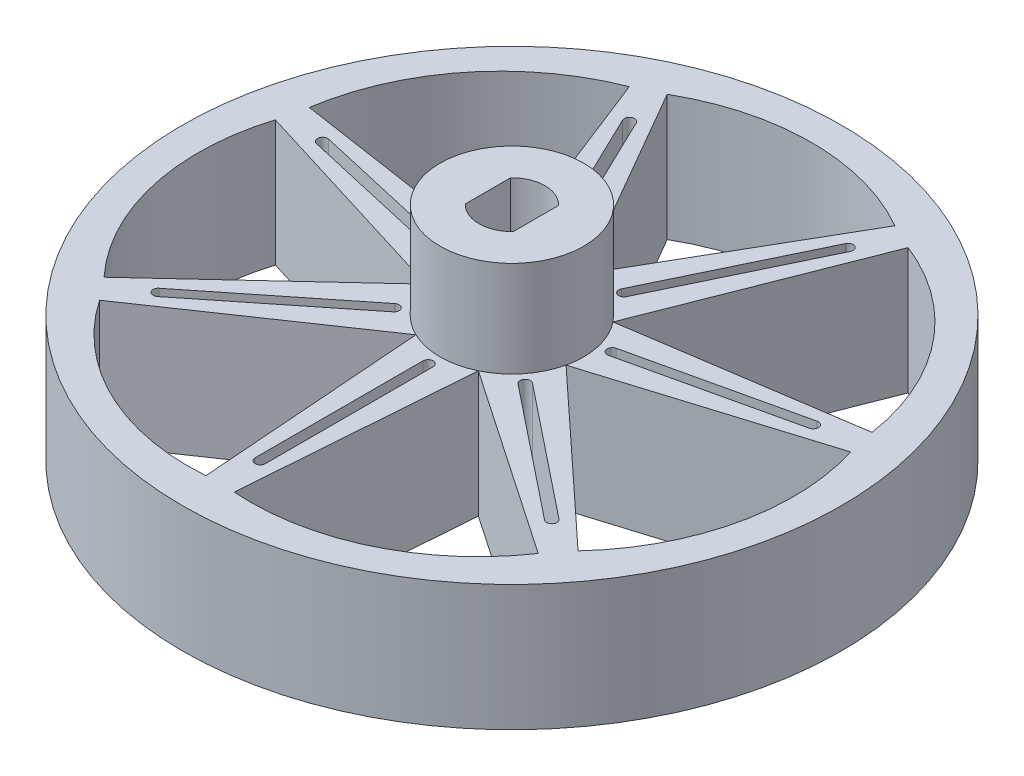
SolidWorks part; units mm, degrees
ref_plane "Front Plane" through (0, 0, 0) normal (0, 0, 1) x (1, 0, 0)
ref_plane "Top Plane" through (0, 0, 0) normal (0, 1, 0) x (1, 0, 0)
ref_plane "Right Plane" through (0, 0, 0) normal (1, 0, 0) x (0, 0, -1)
sketch "Sketch2" plane through (0, 0, 0) normal (0, 1, 0) x (1, 0, 0)
  line L0 (-2, -1.8875) -> (-2, 1.8875)
  line L2 (-1.75, -1.7854) -> (-1.75, 1.7854)
  line L4 (1.75, -1.7854) -> (1.75, 1.7854)
  line L5 (-1.75, -1.7854) -> (1.75, 1.7854) construction
  line L6 (-1.75, 1.7854) -> (1.75, -1.7854) construction
  line L7 (2, -1.8875) -> (2, 1.8875)
  arc A0 (1.75, 1.7854) -> (-1.75, 1.7854) centre (0, 0) ccw
  arc A1 (-1.75, -1.7854) -> (1.75, -1.7854) centre (0, 0) ccw
  circle A2 centre (0, 0) radius 6
  arc A3 (2, 1.8875) -> (-2, 1.8875) centre (0, 0) ccw
  arc A4 (-2, -1.8875) -> (2, -1.8875) centre (0, 0) ccw
  dimension "D1" = 5
  dimension "D3" = 12
  dimension "D2" = 3.5
  dimension "D4" = 0.25
extrude "Boss-Extrude1" add sketch "Sketch2" along normal blind 8 contours A2 A4 L0 A3 L7
sketch "Sketch3" plane through (0, 0, 0) normal (0, 1, 0) x (1, 0, 0)
  line L0 (0, 0) -> (0, 27.5) construction
  line L1 (0, 6) -> (9.5, 22.4545)
  line L2 (0, 6) -> (-9.5, 22.4545)
  line L3 (4.691, 3.7409) -> (11.6325, 21.4275)
  line L4 (4.691, 3.7409) -> (23.4788, 6.5727)
  line L5 (5.8496, -1.3351) -> (24.0055, 4.2652)
  line L6 (5.8496, -1.3351) -> (19.7776, -14.2584)
  line L7 (2.6033, -5.4058) -> (18.3018, -16.1089)
  line L8 (2.6033, -5.4058) -> (1.1834, -24.3527)
  line L9 (-2.6033, -5.4058) -> (-1.1834, -24.3527)
  line L10 (-2.6033, -5.4058) -> (-18.3018, -16.1089)
  line L11 (-5.8496, -1.3351) -> (-19.7776, -14.2584)
  line L12 (-5.8496, -1.3351) -> (-24.0055, 4.2652)
  line L13 (-4.691, 3.7409) -> (-23.4788, 6.5727)
  line L14 (-4.691, 3.7409) -> (-11.6325, 21.4275)
  circle A0 centre (0, 0) radius 1.375
  circle A1 centre (0, 0) radius 27.5
  circle A2 centre (0, 0) radius 6 construction
  arc A3 (9.5, 22.4545) -> (-9.5, 22.4545) centre (0, 6) ccw
  arc A4 (23.4788, 6.5727) -> (11.6325, 21.4275) centre (4.691, 3.7409) ccw
  arc A5 (19.7776, -14.2584) -> (24.0055, 4.2652) centre (5.8496, -1.3351) ccw
  arc A6 (1.1834, -24.3527) -> (18.3018, -16.1089) centre (2.6033, -5.4058) ccw
  arc A7 (-18.3018, -16.1089) -> (-1.1834, -24.3527) centre (-2.6033, -5.4058) ccw
  arc A8 (-24.0055, 4.2652) -> (-19.7776, -14.2584) centre (-5.8496, -1.3351) ccw
  arc A9 (-11.6325, 21.4275) -> (-23.4788, 6.5727) centre (-4.691, 3.7409) ccw
  point P37 (0, 0)
  dimension "D1" = 2.75
  dimension "D2" = 55
  dimension "D3" = 19
  dimension "D4" = 30
  dimension "D5" = 7
extrude "Boss-Extrude2" add sketch "Sketch3" against normal blind 10.5
sketch "Sketch4" plane through (0, -10.5, 0) normal (0, -1, 0) x (-1, 0, 0)
  circle A0 centre (0, 0) radius 3
  dimension "D1" = 6
extrude "Cut-Extrude1" cut sketch "Sketch4" against normal blind 9.5
sketch "Sketch5" plane through (0, 0, 0) normal (0, 1, 0) x (1, 0, 0)
  line L0 (0, -30.3767) -> (0, 0) construction
  line L1 (-5.7393, -4.0303) -> (-16.6849, -12.7592)
  line L2 (0.4274, -7) -> (-0.4274, -7)
  line L3 (0.4274, -7) -> (0.4274, -21)
  line L4 (0.4274, -21) -> (-0.4274, -21)
  line L5 (-0.4274, -7) -> (-0.4274, -21)
  line L6 (0.4274, -7) -> (-0.4274, -21) construction
  line L7 (0.4274, -21) -> (-0.4274, -7) construction
  line L8 (-5.2064, -4.6986) -> (-16.152, -13.4274)
  line L9 (-6.7294, 1.9743) -> (-20.3784, 5.0896)
  line L10 (-6.9196, 1.141) -> (-20.5686, 4.2563)
  line L11 (-2.6521, 6.4922) -> (-8.7265, 19.1058)
  line L12 (-3.4222, 6.1214) -> (-9.4966, 18.7349)
  line L13 (3.4222, 6.1214) -> (9.4966, 18.7349)
  line L14 (2.6521, 6.4922) -> (8.7265, 19.1058)
  line L15 (6.9196, 1.141) -> (20.5686, 4.2563)
  line L16 (6.7294, 1.9743) -> (20.3784, 5.0896)
  line L17 (5.2064, -4.6986) -> (16.152, -13.4274)
  line L18 (5.7393, -4.0303) -> (16.6849, -12.7592)
  circle A0 centre (0, 0) radius 1.375 construction
  arc A1 (-0.4242, -20.948) -> (0.4242, -20.948) centre (0, -21) ccw
  arc A2 (0.4242, -7.052) -> (-0.4242, -7.052) centre (0, -7) ccw
  arc A3 (-16.6423, -12.7292) -> (-16.1133, -13.3925) centre (-16.4185, -13.0933) ccw
  arc A4 (-5.249, -4.7285) -> (-5.7779, -4.0652) centre (-5.4728, -4.3644) ccw
  arc A5 (-20.3284, 5.0749) -> (-20.5172, 4.2478) centre (-20.4735, 4.6729) ccw
  arc A6 (-6.9696, 1.1557) -> (-6.7808, 1.9828) centre (-6.8245, 1.5576) ccw
  arc A7 (-8.7068, 19.0576) -> (-9.4712, 18.6895) centre (-9.1116, 18.9203) ccw
  arc A8 (-3.4419, 6.1696) -> (-2.6776, 6.5377) centre (-3.0372, 6.3068) ccw
  arc A9 (9.4712, 18.6895) -> (8.7068, 19.0576) centre (9.1116, 18.9203) ccw
  arc A10 (2.6776, 6.5377) -> (3.4419, 6.1696) centre (3.0372, 6.3068) ccw
  arc A11 (20.5172, 4.2478) -> (20.3284, 5.0749) centre (20.4735, 4.6729) ccw
  arc A12 (6.7808, 1.9828) -> (6.9696, 1.1557) centre (6.8245, 1.5576) ccw
  arc A13 (16.1133, -13.3925) -> (16.6423, -12.7292) centre (16.4185, -13.0933) ccw
  arc A14 (5.7779, -4.0652) -> (5.249, -4.7285) centre (5.4728, -4.3644) ccw
  point P2 (0, -14)
  point P79 (0, 0)
  dimension "D1" = 7
  dimension "D3" = 14
  dimension "D2" = 7
extrude "Cut-Extrude2" cut sketch "Sketch5" against normal up to next
